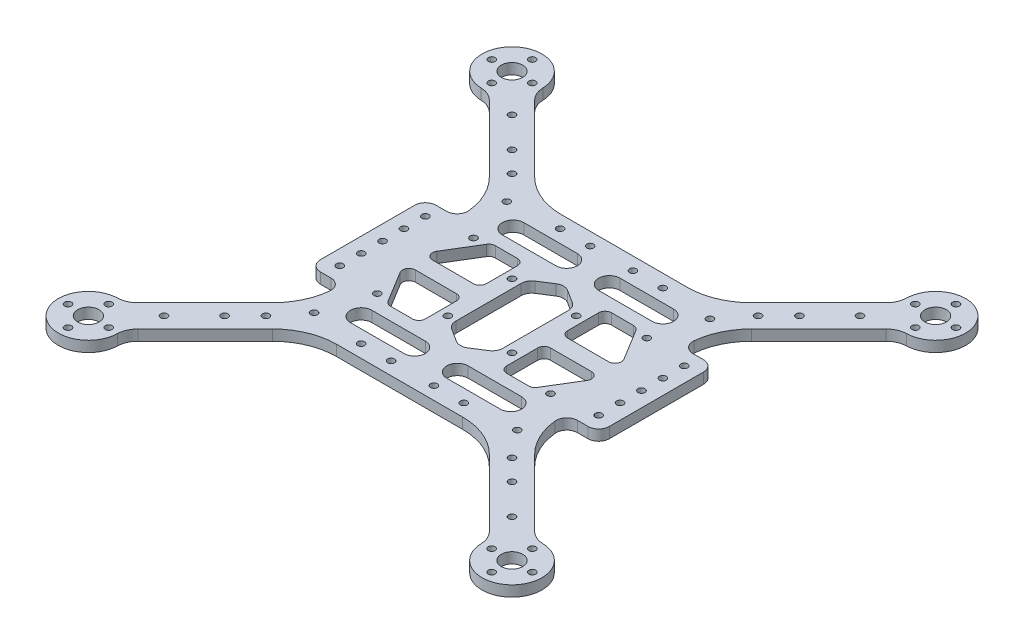
SolidWorks part; units mm, degrees
ref_plane "前视基准面" through (0, 0, 0) normal (0, 0, 1) x (1, 0, 0)
ref_plane "上视基准面" through (0, 0, 0) normal (0, 1, 0) x (1, 0, 0)
ref_plane "右视基准面" through (0, 0, 0) normal (1, 0, 0) x (0, 0, -1)
sketch "草图1" plane through (0, 0, 0) normal (0, 1, 0) x (1, 0, 0)
  line L0 (0, -17.853) -> (0, -37.4252) construction
  line L1 (-41.8934, -52.5) -> (41.8934, -52.5)
  line L2 (-52.5, -41.8934) -> (-52.5, 41.8934)
  line L3 (-41.8934, 52.5) -> (41.8934, 52.5)
  line L4 (52.5, -41.8934) -> (52.5, 41.8934)
  line L5 (-52.5, -52.5) -> (52.5, 52.5) construction
  line L6 (-52.5, 52.5) -> (52.5, -52.5) construction
  line L7 (24.333, 0) -> (44.1697, 0) construction
  line L8 (-52.5, 41.8934) -> (-95.9391, 85.3325)
  line L9 (-41.8934, 52.5) -> (-85.3325, 95.9391)
  line L10 (41.8934, 52.5) -> (85.3325, 95.9391)
  line L11 (52.5, 41.8934) -> (95.9391, 85.3325)
  line L12 (-41.8934, -52.5) -> (-85.3325, -95.9391)
  line L13 (-52.5, -41.8934) -> (-95.9391, -85.3325)
  line L14 (41.8934, -52.5) -> (85.3325, -95.9391)
  line L15 (52.5, -41.8934) -> (95.9391, -85.3325)
  circle A0 centre (-47.5, 45) radius 1.6
  circle A1 centre (47.5, 45) radius 1.6
  circle A2 centre (-47.5, -45) radius 1.6
  circle A3 centre (47.5, -45) radius 1.6
  arc A4 (-85.3325, 95.9391) -> (-95.9391, 85.3325) centre (-98.9949, 98.9949) ccw
  circle A12 centre (-98.9949, 98.9949) radius 9.5 construction
  circle A13 centre (-98.9949, 108.4949) radius 1.6
  circle A14 centre (-89.4949, 98.9949) radius 1.6
  circle A15 centre (-98.9949, 89.4949) radius 1.6
  circle A16 centre (-108.4949, 98.9949) radius 1.6
  circle A17 centre (-98.9949, 98.9949) radius 5
  circle A18 centre (108.4949, 98.9949) radius 1.6
  circle A19 centre (98.9949, 89.4949) radius 1.6
  circle A20 centre (89.4949, 98.9949) radius 1.6
  circle A21 centre (98.9949, 108.4949) radius 1.6
  circle A22 centre (98.9949, 98.9949) radius 5
  arc A23 (85.3325, 95.9391) -> (95.9391, 85.3325) centre (98.9949, 98.9949) cw
  circle A24 centre (-89.4949, -98.9949) radius 1.6
  circle A25 centre (-98.9949, -108.4949) radius 1.6
  circle A26 centre (-98.9949, -98.9949) radius 5
  circle A27 centre (-98.9949, -89.4949) radius 1.6
  circle A28 centre (-108.4949, -98.9949) radius 1.6
  arc A29 (-85.3325, -95.9391) -> (-95.9391, -85.3325) centre (-98.9949, -98.9949) cw
  circle A30 centre (98.9949, -89.4949) radius 1.6
  circle A31 centre (108.4949, -98.9949) radius 1.6
  circle A32 centre (98.9949, -108.4949) radius 1.6
  circle A33 centre (98.9949, -98.9949) radius 5
  circle A34 centre (89.4949, -98.9949) radius 1.6
  arc A35 (85.3325, -95.9391) -> (95.9391, -85.3325) centre (98.9949, -98.9949) ccw
  circle A36 centre (-67.1751, 67.1751) radius 1.6
  circle A37 centre (-81.3173, 81.3173) radius 1.6
  circle A38 centre (-67.1751, -67.1751) radius 1.6
  circle A39 centre (-81.3173, -81.3173) radius 1.6
  circle A40 centre (67.1751, -67.1751) radius 1.6
  circle A41 centre (81.3173, -81.3173) radius 1.6
  circle A42 centre (67.1751, 67.1751) radius 1.6
  circle A43 centre (81.3173, 81.3173) radius 1.6
  point P0 (0, 0)
  point P40 (-98.9949, 98.9949)
  dimension "D5" = 3.2
  dimension "D7" = 28
  dimension "D9" = 19
  dimension "D10" = 4
  dimension "D11" = 3.2
  dimension "D12" = 10
  dimension "D1" = 105
  dimension "D2" = 105
  dimension "D3" = 95
  dimension "D4" = 90
  dimension "D6" = 140
  dimension "D8" = 15
  dimension "D13" = 20
  dimension "D14" = 25
extrude "凸台-拉伸1" add sketch "草图1" along normal blind 5
sketch "草图2" plane through (0, 5, 0) normal (0, 1, 0) x (1, 0, 0)
  line L0 (0, -4.1752) -> (0, -17.8791) construction
  line L1 (8.7881, 0) -> (32.8781, 0) construction
  line L12 (-52.5, 41.8934) -> (-52.5, -41.8934) construction
  line L49 (-10, 35.5) -> (-35, 35.5) construction
  line L50 (-11, 18) -> (-11, -18)
  line L51 (-11, 18) -> (0, 25)
  line L52 (11, 18) -> (11, -18)
  line L53 (11, 18) -> (0, 25)
  line L54 (11, -18) -> (0, -25)
  line L55 (-11, -18) -> (0, -25)
  line L56 (-10, 30.5) -> (-35, 30.5)
  line L59 (-10, 40.5) -> (-35, 40.5)
  line L60 (41.8934, 52.5) -> (-41.8934, 52.5) construction
  line L61 (10, 35.5) -> (35, 35.5) construction
  line L62 (10, 30.5) -> (35, 30.5)
  line L63 (10, 40.5) -> (35, 40.5)
  line L64 (-10, -35.5) -> (-35, -35.5) construction
  line L65 (-10, -30.5) -> (-35, -30.5)
  line L66 (-10, -40.5) -> (-35, -40.5)
  line L67 (10, -35.5) -> (35, -35.5) construction
  line L68 (10, -30.5) -> (35, -30.5)
  line L69 (10, -40.5) -> (35, -40.5)
  line L70 (-46.5, 4) -> (-19, 4)
  line L71 (-19, 4) -> (-19, 24.5)
  line L72 (-19, 24.5) -> (-34, 24.5)
  line L73 (-34, 24.5) -> (-46.5, 4)
  line L74 (-19, -24.5) -> (-34, -24.5)
  line L75 (-19, -4) -> (-19, -24.5)
  line L76 (-46.5, -4) -> (-19, -4)
  line L77 (-34, -24.5) -> (-46.5, -4)
  line L78 (19, -4) -> (19, -24.5)
  line L79 (46.5, -4) -> (19, -4)
  line L80 (34, -24.5) -> (46.5, -4)
  line L81 (19, -24.5) -> (34, -24.5)
  line L82 (19, 24.5) -> (34, 24.5)
  line L83 (19, 4) -> (19, 24.5)
  line L84 (46.5, 4) -> (19, 4)
  line L85 (34, 24.5) -> (46.5, 4)
  circle A0 centre (-40.5, 22.5) radius 1.6
  circle A1 centre (-40.5, -22.5) radius 1.6
  circle A2 centre (40.5, -22.5) radius 1.6
  circle A3 centre (40.5, 22.5) radius 1.6
  arc A6 (-10, 30.5) -> (-10, 40.5) centre (-10, 35.5) ccw
  arc A7 (-35, 40.5) -> (-35, 30.5) centre (-35, 35.5) ccw
  arc A8 (10, 30.5) -> (10, 40.5) centre (10, 35.5) cw
  arc A9 (35, 40.5) -> (35, 30.5) centre (35, 35.5) cw
  arc A10 (-10, -30.5) -> (-10, -40.5) centre (-10, -35.5) cw
  arc A11 (-35, -40.5) -> (-35, -30.5) centre (-35, -35.5) cw
  arc A12 (10, -30.5) -> (10, -40.5) centre (10, -35.5) ccw
  arc A13 (35, -40.5) -> (35, -30.5) centre (35, -35.5) ccw
  circle A14 centre (-24, 46.5) radius 1.6
  circle A15 centre (24, 46.5) radius 1.6
  circle A16 centre (24, -46.5) radius 1.6
  circle A17 centre (-24, -46.5) radius 1.6
  circle A18 centre (-15, 15) radius 1.6
  circle A19 centre (15, 15) radius 1.6
  circle A20 centre (15, -15) radius 1.6
  circle A21 centre (-15, -15) radius 1.6
  circle A22 centre (-10, 46.5) radius 1.6
  circle A23 centre (10, 46.5) radius 1.6
  circle A24 centre (10, -46.5) radius 1.6
  circle A25 centre (-10, -46.5) radius 1.6
  point P37 (0, 32.5)
  point P39 (11, 0)
  point P41 (-11, 0)
  point P43 (-22.5, 35.5)
  point P48 (-22.5, 0)
  point P53 (22.5, 35.5)
  point P60 (-22.5, -35.5)
  point P67 (22.5, -35.5)
  dimension "D5" = 3.2
  dimension "D11" = 12
  dimension "D13" = 5
  dimension "D21" = 20
  dimension "D2" = 8
  dimension "D3" = 48
  dimension "D4" = 45
  dimension "D6" = 12
  dimension "D7" = 6
  dimension "D8" = 22
  dimension "D9" = 36
  dimension "D10" = 50
  dimension "D12" = 25
  dimension "D14" = 45
  dimension "D15" = 6
  dimension "D16" = 30
  dimension "D17" = 6
  dimension "D18" = 8
  dimension "D19" = 15
  dimension "D20" = 30
extrude "切除-拉伸1" cut sketch "草图2" against normal through all
sketch "草图3" plane through (0, 5, 0) normal (0, 1, 0) x (1, 0, 0)
  line L0 (0, -8.0185) -> (0, -27.3056) construction
  line L1 (31.7277, 0) -> (48.677, 0) construction
  line L2 (-52.5, 41.8934) -> (-52.5, -41.8934) construction
  line L3 (-52.5, 27) -> (-67.5, 27)
  line L4 (-52.5, 27) -> (-52.5, -27)
  line L5 (-52.5, -27) -> (-67.5, -27)
  line L6 (-67.5, 27) -> (-67.5, -27)
  line L7 (67.5, 27) -> (67.5, -27)
  line L8 (52.5, -27) -> (67.5, -27)
  line L9 (52.5, 27) -> (52.5, -27)
  line L10 (52.5, 27) -> (67.5, 27)
  circle A0 centre (-60.5, 20) radius 1.6
  circle A2 centre (-60.5, -20) radius 1.6
  circle A3 centre (60.5, -20) radius 1.6
  circle A5 centre (60.5, 20) radius 1.6
  circle A6 centre (-60.5, 10) radius 1.6
  circle A7 centre (-60.5, -10) radius 1.6
  circle A8 centre (60.5, -10) radius 1.6
  circle A9 centre (60.5, 10) radius 1.6
  circle A10 centre (-60.5, 0) radius 1.6
  circle A11 centre (60.5, 0) radius 1.6
  dimension "D4" = 3.2
  dimension "D1" = 54
  dimension "D2" = 15
  dimension "D3" = 8
  dimension "D5" = 20
  dimension "D6" = 20
extrude "凸台-拉伸2" add sketch "草图3" against normal up to surface (5 mm away) up to face at (-15, 0, -13.4)
fillet "圆角1" radius 30 8 edges at (-52.5, 2.5, 41.8934) (-41.8934, 2.5, 52.5) (41.8934, 2.5, 52.5) (52.5, 2.5, 41.8934) (52.5, 2.5, -41.8934) (41.8934, 2.5, -52.5) (-41.8934, 2.5, -52.5) (-52.5, 2.5, -41.8934)
fillet "圆角2" radius 10 8 edges at (-85.3325, 2.5, -95.9391) (-95.9391, 2.5, -85.3325) (95.9391, 2.5, -85.3325) (85.3325, 2.5, -95.9391) (85.3325, 2.5, 95.9391) (95.9391, 2.5, 85.3325) (-95.9391, 2.5, 85.3325) (-85.3325, 2.5, 95.9391)
fillet "圆角3" radius 5 4 edges at (-67.5, 2.5, 27) (-67.5, 2.5, -27) (67.5, 2.5, 27) (67.5, 2.5, -27)
fillet "圆角4" radius 5 4 edges at (-52.5, 2.5, 27) (-52.5, 2.5, -27) (52.5, 2.5, -27) (52.5, 2.5, 27)
fillet "圆角5" radius 5 6 edges at (-11, 2.5, 18) (0, 2.5, 25) (11, 2.5, 18) (11, 2.5, -18) (-11, 2.5, -18) (0, 2.5, -25)
fillet "圆角6" radius 3 16 edges at (-34, 2.5, 24.5) (-19, 2.5, 24.5) (-19, 2.5, 4) (-46.5, 2.5, 4) (-19, 2.5, -4) (-19, 2.5, -24.5) (-34, 2.5, -24.5) (-46.5, 2.5, -4) (46.5, 2.5, -4) (34, 2.5, 24.5) (19, 2.5, 24.5) (19, 2.5, -4) (46.5, 2.5, 4) (34, 2.5, -24.5) (19, 2.5, 4) (19, 2.5, -24.5)
sketch "草图4" plane through (0, 5, 0) normal (0, 1, 0) x (1, 0, 0)
  line L1 (-52.5, -52.5) -> (52.5, -52.5) construction
  line L2 (-52.5, -52.5) -> (-52.5, 52.5) construction
  line L3 (-52.5, 52.5) -> (52.5, 52.5) construction
  line L4 (52.5, -52.5) -> (52.5, 52.5) construction
  line L5 (-52.5, -52.5) -> (52.5, 52.5) construction
  line L6 (-52.5, 52.5) -> (52.5, -52.5) construction
  line L7 (-57.5, -57.5) -> (57.5, -57.5) construction
  line L8 (-57.5, -57.5) -> (-57.5, 57.5) construction
  line L9 (-57.5, 57.5) -> (57.5, 57.5) construction
  line L10 (57.5, -57.5) -> (57.5, 57.5) construction
  line L11 (-57.5, -57.5) -> (57.5, 57.5) construction
  line L12 (-57.5, 57.5) -> (57.5, -57.5) construction
  circle A0 centre (-57.5, 57.5) radius 1.6
  circle A1 centre (57.5, 57.5) radius 1.6
  circle A2 centre (-57.5, -57.5) radius 1.6
  circle A3 centre (57.5, -57.5) radius 1.6
  point P0 (0, 0)
  point P6 (0, 0)
extrude "切除-拉伸2" cut sketch "草图4" against normal through all
sketch "草图5" plane through (0, 5, 0) normal (0, 1, 0) x (1, 0, 0)
  circle A0 centre (0, 17) radius 1
  circle A1 centre (30, 17) radius 1
  circle A2 centre (30, -17) radius 1
  circle A3 centre (0, -17) radius 1
  dimension "D1" = 2
  dimension "D4" = 17
  dimension "D5" = 34
  dimension "D6" = 0
  dimension "D2" = 2
  dimension "D3" = 2
